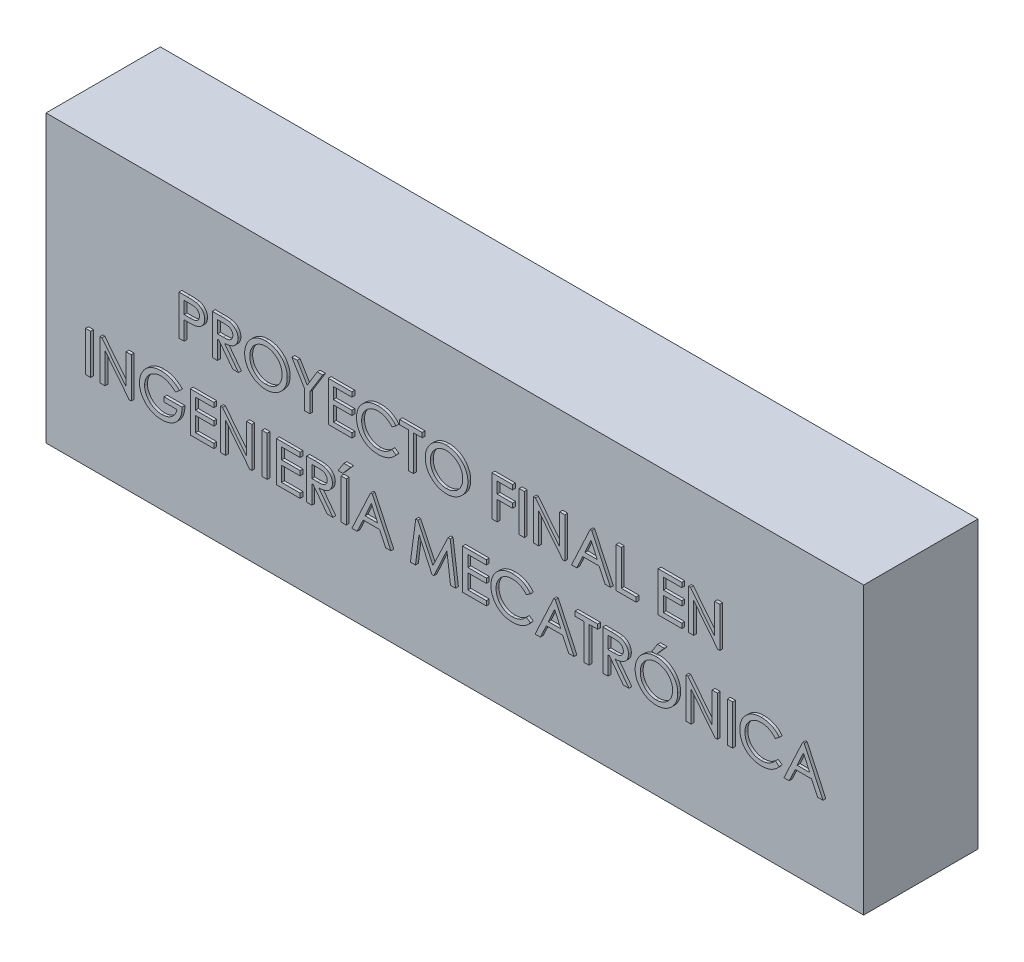
SolidWorks part; units mm, degrees
ref_plane "Front Plane" through (0, 0, 0) normal (0, 0, 1) x (1, 0, 0)
ref_plane "Top Plane" through (0, 0, 0) normal (0, 1, 0) x (1, 0, 0)
ref_plane "Right Plane" through (0, 0, 0) normal (1, 0, 0) x (0, 0, -1)
sketch "Croquis1" plane through (0, 0, 0) normal (0, 0, 1) x (1, 0, 0)
  line L1 (-35.75, 12.5) -> (35.75, 12.5)
  line L2 (-35.75, 12.5) -> (-35.75, -12.5)
  line L3 (-35.75, -12.5) -> (35.75, -12.5)
  line L4 (35.75, 12.5) -> (35.75, -12.5)
  line L5 (-35.75, 12.5) -> (35.75, -12.5) construction
  line L6 (-35.75, -12.5) -> (35.75, 12.5) construction
  point P0 (0, 0)
  dimension "D1" = 25
  dimension "D2" = 71.5
extrude "Saliente-Extruir1" add sketch "Croquis1" along normal blind 10
sketch "Croquis2" plane through (0, 0, 10) normal (0, 0, 1) x (1, 0, 0)
  line L0 (35.75, 0) -> (-35.75, 0) construction
  line L1 (35.75, -12.5) -> (35.75, 12.5) construction
  line L2 (-35.75, 12.5) -> (-35.75, -12.5) construction
  line L3 (35.75, 1.5) -> (-35.75, 1.5) construction
  text T0 "<b>PROYECTO FINAL EN</b>\r\n<b>INGENIERÍA MECATRÓNICA</b>"
  dimension "D1" = 1.5
extrude "Saliente-Extruir2" add sketch "Croquis2" along normal blind 0.25
